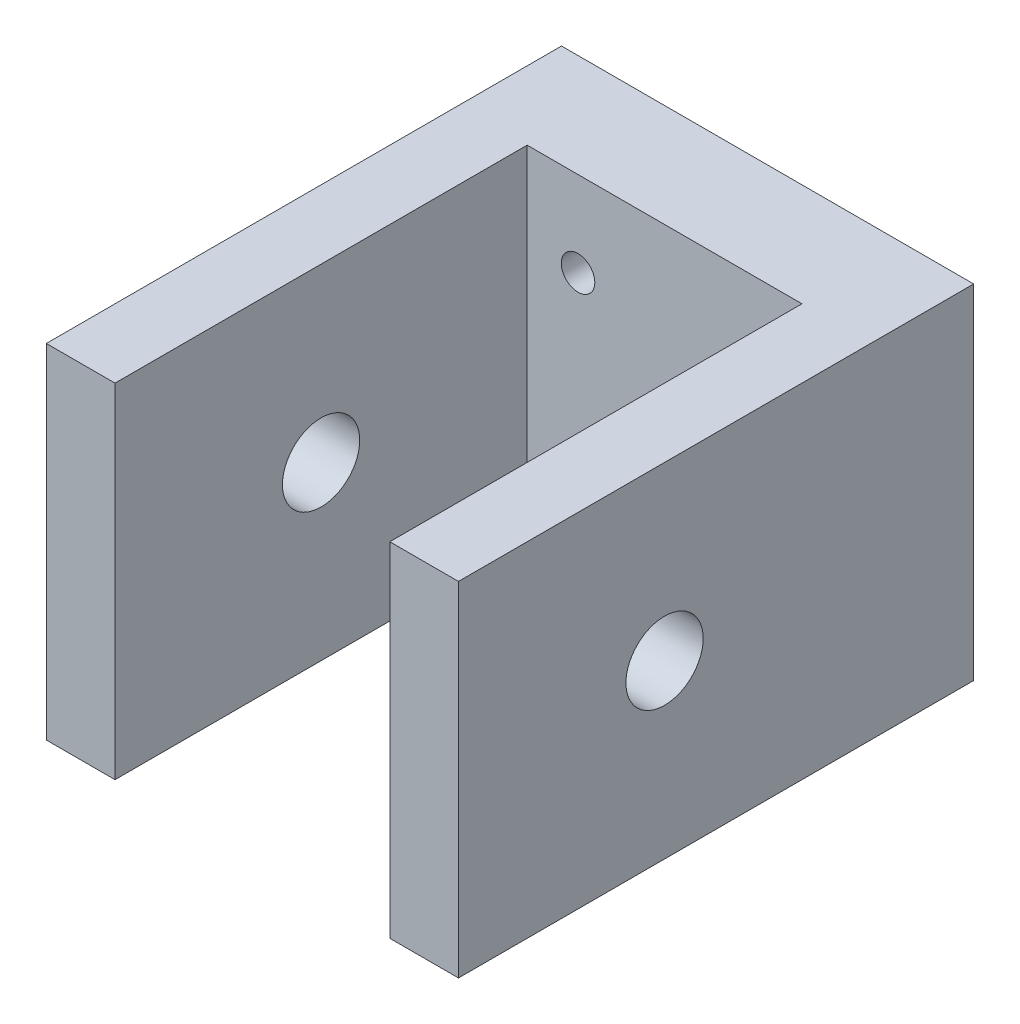
SolidWorks part; units mm, degrees
material "Onyx w/ CF"
ref_plane "Front Plane" through (0, 0, 0) normal (0, 0, 1) x (1, 0, 0)
ref_plane "Top Plane" through (0, 0, 0) normal (0, 1, 0) x (1, 0, 0)
ref_plane "Right Plane" through (0, 0, 0) normal (1, 0, 0) x (0, 0, -1)
sketch "Sketch2" plane through (0, 0, 0) normal (0, 1, 0) x (1, 0, 0)
  line L0 (-12.7, 0) -> (-12.7, -38.1)
  line L1 (-12.7, -38.1) -> (-19.05, -38.1)
  line L2 (-19.05, -38.1) -> (-19.05, 9.525)
  line L3 (-19.05, 9.525) -> (19.05, 9.525)
  line L4 (19.05, 9.525) -> (19.05, -38.1)
  line L5 (19.05, -38.1) -> (12.7, -38.1)
  line L6 (12.7, -38.1) -> (12.7, 0)
  line L7 (12.7, 0) -> (-12.7, 0)
  point P9 (0, 0)
  dimension "D1" = 25.4
  dimension "D2" = 6.35
  dimension "D3" = 9.525
  dimension "D4" = 38.1
extrude "Boss-Extrude1" add sketch "Sketch2" along normal mid plane 31.75
hole_wizard "M2.5 Clearance Hole1" positions "Sketch3" profile "Sketch4" hole size "M2.5" standard "ANSI Metric" end condition through all
sketch "Sketch3" plane through (0, 0, -9.525) normal (0, 0, -1) x (-1, 0, 0)
  line L1 (8, -8) -> (-8, -8)
  line L2 (8, -8) -> (8, 8)
  line L3 (8, 8) -> (-8, 8)
  line L4 (-8, -8) -> (-8, 8)
  line L5 (8, -8) -> (-8, 8) construction
  line L6 (8, 8) -> (-8, -8) construction
  point P0 (8, 8)
  point P2 (-8, 8)
  point P4 (-8, -8)
  point P6 (8, -8)
  point P60 (0, 0)
  dimension "D1" = 16
sketch "Sketch4" plane through (-8, 8, -9.525) normal (1, 0, 0) x (0, 1, 0)
  line L0 (0, 0) -> (0, 47.625)
  line L1 (0, 47.625) -> (1.55, 47.625)
  line L2 (1.55, 47.625) -> (1.55, 0)
  line L5 (1.55, 0) -> (0, 0)
  line L11 (0, -6.35) -> (0, 107.95) construction
  dimension "Thru Hole Dia." = 3.1
  dimension "Thru Hole Depth" = 47.625
hole_wizard "1/4 Clearance Hole1" positions "Sketch5" profile "Sketch6" hole size "1/4" standard "ANSI Inch" end condition through all
sketch "Sketch5" plane through (19.05, 0, 0) normal (1, 0, 0) x (0, 0, -1)
  line L0 (0, -15.875) -> (-38.1, -15.875) construction
  point P0 (-19.05, 0)
  point P5 (-19.05, -15.875)
sketch "Sketch6" plane through (19.05, 0, 19.05) normal (0, 1, 0) x (0, 0, -1)
  line L0 (0, 0) -> (0, 38.1)
  line L1 (0, 38.1) -> (3.5712, 38.1)
  line L2 (3.5712, 38.1) -> (3.5712, 0)
  line L5 (3.5712, 0) -> (0, 0)
  line L11 (0, -6.35) -> (0, 107.95) construction
  dimension "Thru Hole Dia." = 7.1425
  dimension "Thru Hole Depth" = 38.1
ref_plane "Plane1" through (0, 0, -4.7625) normal (0, 0, 1) x (1, 0, 0)
sketch "Sketch7" plane through (0, 0, -4.7625) normal (0, 0, 1) x (1, 0, 0)
  line L1 (11.0734, 10.7241) -> (4.9266, 10.7241)
  line L2 (11.0734, 10.7241) -> (11.0734, 5.2758)
  line L3 (11.0734, 5.2758) -> (4.9266, 5.2758)
  line L4 (4.9266, 10.7241) -> (4.9266, 5.2758)
  line L5 (11.0734, 10.7241) -> (4.9266, 5.2758) construction
  line L6 (11.0734, 5.2758) -> (4.9266, 10.7241) construction
  line L7 (-4.9266, 10.7241) -> (-11.0734, 10.7241)
  line L8 (-4.9266, 10.7241) -> (-4.9266, 5.2758)
  line L9 (-4.9266, 5.2758) -> (-11.0734, 5.2758)
  line L10 (-11.0734, 10.7241) -> (-11.0734, 5.2758)
  line L11 (-4.9266, 10.7241) -> (-11.0734, 5.2758) construction
  line L12 (-4.9266, 5.2758) -> (-11.0734, 10.7241) construction
  line L13 (-4.9266, -5.2759) -> (-11.0734, -5.2759)
  line L14 (-4.9266, -5.2759) -> (-4.9266, -10.7242)
  line L15 (-4.9266, -10.7242) -> (-11.0734, -10.7242)
  line L16 (-11.0734, -5.2759) -> (-11.0734, -10.7242)
  line L17 (-4.9266, -5.2759) -> (-11.0734, -10.7242) construction
  line L18 (-4.9266, -10.7242) -> (-11.0734, -5.2759) construction
  line L19 (11.0734, -5.2759) -> (4.9266, -5.2759)
  line L20 (11.0734, -5.2759) -> (11.0734, -10.7242)
  line L21 (11.0734, -10.7242) -> (4.9266, -10.7242)
  line L22 (4.9266, -5.2759) -> (4.9266, -10.7242)
  line L23 (11.0734, -5.2759) -> (4.9266, -10.7242) construction
  line L24 (11.0734, -10.7242) -> (4.9266, -5.2759) construction
  point P0 (8, 8)
  point P6 (-8, 8)
  point P12 (-8, -8)
  point P18 (8, -8)
  dimension "D1" = 6.1468
  dimension "D2" = 5.4483
extrude "Cut-Extrude1" cut sketch "Sketch7" against normal mid plane 2.3542
